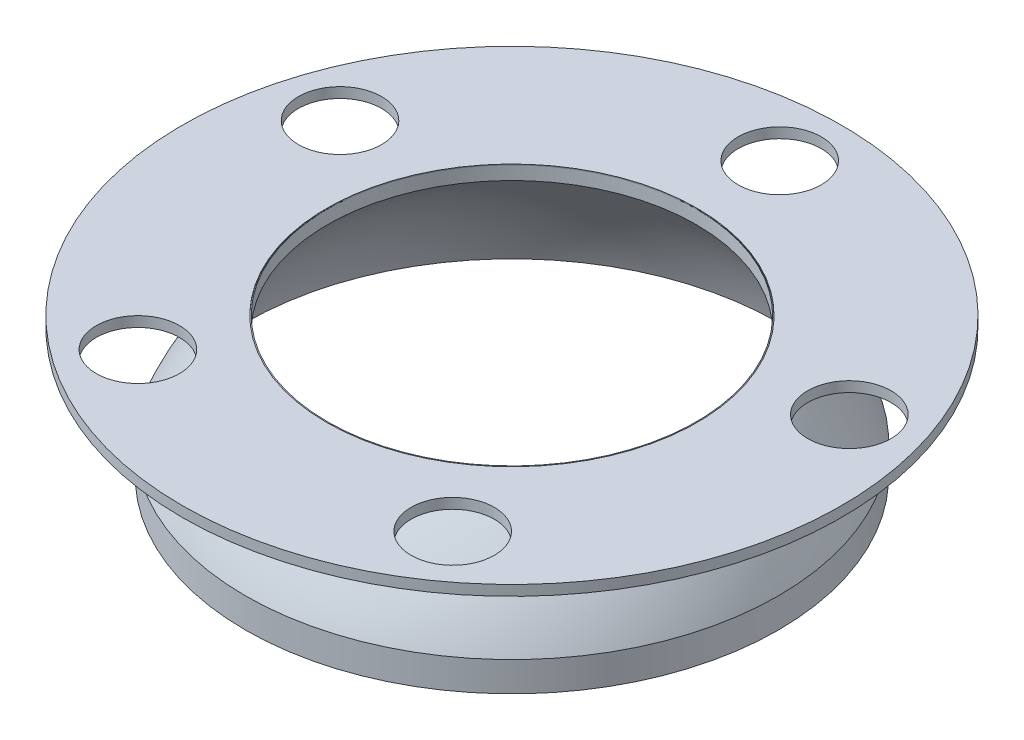
SolidWorks part; units mm, degrees
ref_plane "Front Plane" through (0, 0, 0) normal (0, 0, 1) x (1, 0, 0)
ref_plane "Top Plane" through (0, 0, 0) normal (0, 1, 0) x (1, 0, 0)
ref_plane "Right Plane" through (0, 0, 0) normal (1, 0, 0) x (0, 0, -1)
sketch "Sketch1" plane through (0, -65.6894, 0) normal (1, 0, 0) x (0, 0, -1)
  line L2 (0, 0) -> (0, 109.7865) construction
  line L4 (-82.1256, 25.8904) -> (-82.1256, 35.0313)
  line L5 (-56.8351, 64.6893) -> (-56.8351, 68.8592)
  arc A1 (-56.8351, 64.6893) -> (-82.1256, 25.8904) centre (0, 0) ccw
  arc A4 (-56.8351, 68.8592) -> (-82.1256, 35.0313) centre (0, 0) ccw
  dimension "D1" = 86.11
  dimension "D2" = 3.175
revolve "Revolve1" add sketch "Sketch1" angle 360 about L2
sketch "Sketch2" plane through (0, 0, 0) normal (0, 1, 0) x (1, 0, 0)
  circle A0 centre (0, 0) radius 101.6
  circle A1 centre (0, 82.55) radius 12.827
  circle A2 centre (78.5097, 25.5094) radius 12.827
  circle A3 centre (48.5217, -66.7844) radius 12.827
  circle A4 centre (-48.5217, -66.7844) radius 12.827
  circle A5 centre (-78.5097, 25.5094) radius 12.827
  circle A7 centre (0, 0) radius 57.15
  point P16 (0, 0)
  dimension "D1" = 203.2
  dimension "D2" = 82.55
  dimension "D3" = 25.654
  dimension "D4" = 5
extrude "Boss-Extrude1" add sketch "Sketch2" along normal blind 3.175 separate body contours A0 A7 A5 A4 A3 A2 A1
